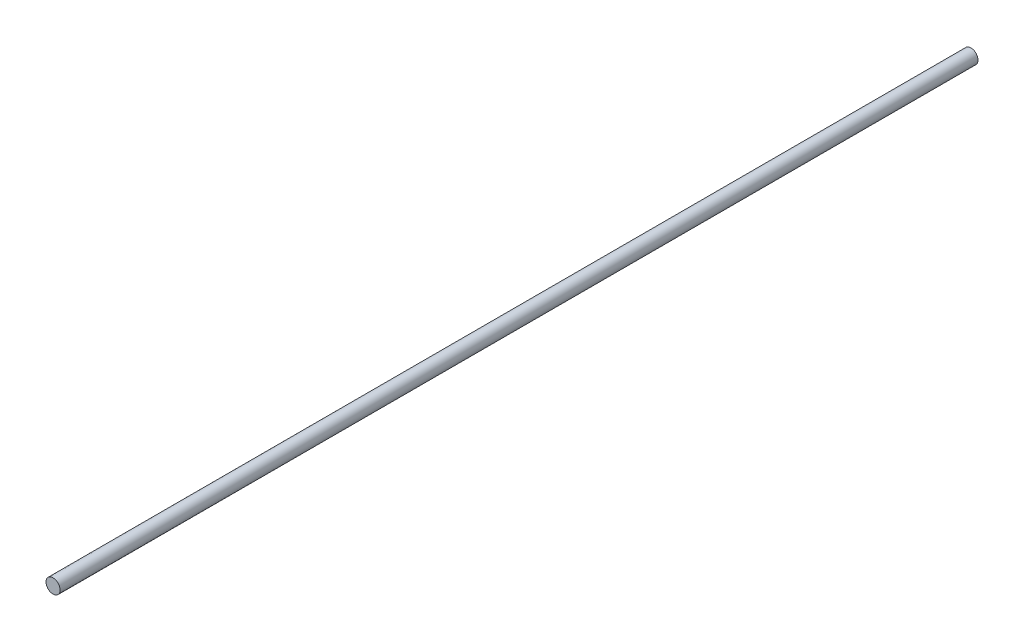
SolidWorks part; units mm, degrees
ref_plane "Front Plane" through (0, 0, 0) normal (0, 0, 1) x (1, 0, 0)
ref_plane "Top Plane" through (0, 0, 0) normal (0, 1, 0) x (1, 0, 0)
ref_plane "Right Plane" through (0, 0, 0) normal (1, 0, 0) x (0, 0, -1)
sketch "Sketch1" plane through (0, 0, 0) normal (0, 0, 1) x (1, 0, 0)
  circle A0 centre (-0.7269, 0.5614) radius 1.1
  dimension "D1" = 2.2
extrude "Boss-Extrude2" add sketch "Sketch1" along normal blind 130 and the other way blind 13
